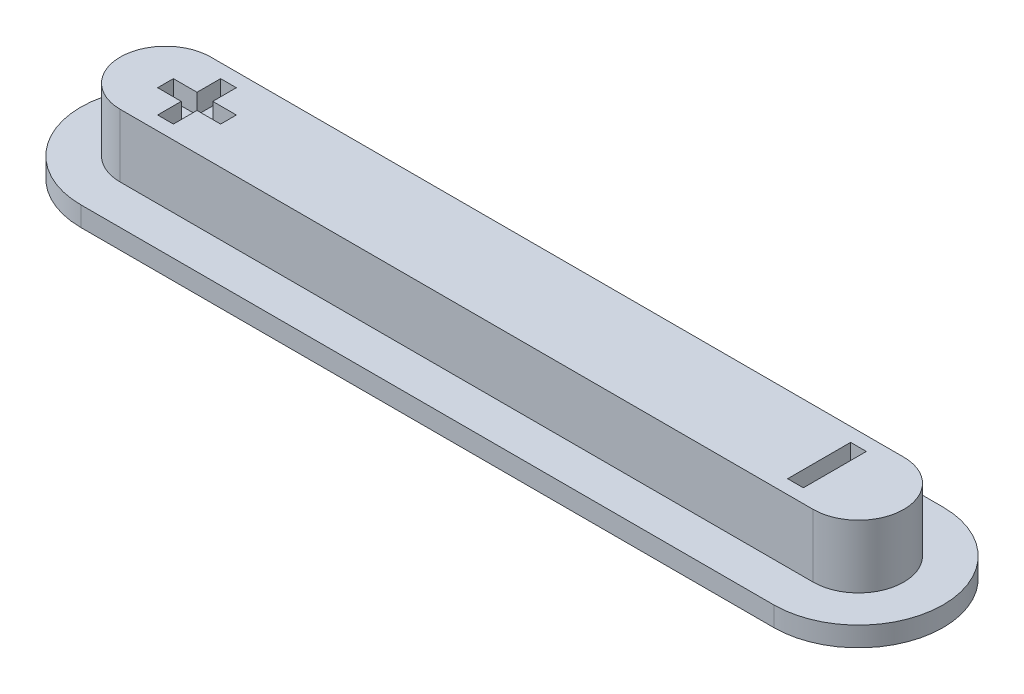
SolidWorks part; units mm, degrees
ref_plane "前视基准面" through (0, 0, 0) normal (0, 0, 1) x (1, 0, 0)
ref_plane "上视基准面" through (0, 0, 0) normal (0, 1, 0) x (1, 0, 0)
ref_plane "右视基准面" through (0, 0, 0) normal (1, 0, 0) x (0, 0, -1)
sketch "草图1" plane through (0, 0, 0) normal (0, 1, 0) x (1, 0, 0)
  line L0 (-8.8, 0) -> (8.8, 0) construction
  line L1 (-8.8, 1.15) -> (8.8, 1.15)
  line L2 (-8.8, -1.15) -> (8.8, -1.15)
  arc A0 (-8.8, 1.15) -> (-8.8, -1.15) centre (-8.8, 0) ccw
  arc A1 (8.8, -1.15) -> (8.8, 1.15) centre (8.8, 0) ccw
  point P2 (0, 0)
extrude "凸台-拉伸1" add sketch "草图1" along normal blind 1.6
sketch "草图2" plane through (0, 0, 0) normal (0, -1, 0) x (1, 0, 0)
  line L4 (-8.8, -2.15) -> (8.8, -2.15)
  line L5 (8.8, 2.15) -> (-8.8, 2.15)
  line L6 (-8.8, -2.15) -> (8.8, -2.15)
  line L7 (8.8, 2.15) -> (-8.8, 2.15)
  arc A4 (-8.8, 2.15) -> (-8.8, -2.15) centre (-8.8, 0) ccw
  arc A5 (8.8, -2.15) -> (8.8, 2.15) centre (8.8, 0) ccw
  arc A6 (-8.8, 2.15) -> (-8.8, -2.15) centre (-8.8, 0) ccw
  arc A7 (8.8, -2.15) -> (8.8, 2.15) centre (8.8, 0) ccw
  dimension "D1" = 1
extrude "凸台-拉伸2" add sketch "草图2" along normal blind 0.5
sketch "草图3" plane through (0, 1.6, 0) normal (0, 1, 0) x (1, 0, 0)
  line L0 (8.8, 1.15) -> (-8.8, 1.15) construction
  line L1 (-8.2, 0.8) -> (-7.8, 0.8)
  line L2 (-8.2, 0.8) -> (-8.2, -0.8)
  line L3 (-8.2, -0.8) -> (-7.8, -0.8)
  line L4 (-7.8, 0.8) -> (-7.8, -0.8)
  line L5 (-8.8, 0.2) -> (-7.2, 0.2)
  line L6 (-8.8, 0.2) -> (-8.8, -0.2)
  line L7 (-8.8, -0.2) -> (-7.2, -0.2)
  line L8 (-7.2, 0.2) -> (-7.2, -0.2)
  line L9 (7.8, 0.8) -> (8.2, 0.8)
  line L10 (7.8, 0.8) -> (7.8, -0.8)
  line L11 (7.8, -0.8) -> (8.2, -0.8)
  line L12 (8.2, 0.8) -> (8.2, -0.8)
  line L13 (-8.8, -1.15) -> (8.8, -1.15) construction
  point P12 (-8, -0.2)
  point P14 (-7.8, 0)
  dimension "D1" = 1.6
  dimension "D2" = 1.6
  dimension "D3" = 1.6
  dimension "D4" = 0.2
  dimension "D5" = 0.4
  dimension "D6" = 0.4
  dimension "D7" = 0.2
  dimension "D8" = 0.35
  dimension "D9" = 0
  dimension "D10" = 0.4
  dimension "D11" = 0.35
  dimension "D12" = 1
extrude "切除-拉伸1" cut sketch "草图3" against normal blind 0.5 contours L12 L9 L10 L11 | L6 L7 L2 L5 | L2 L7 L4 L5 | L2 L5 L4 L1 | L8 L5 L4 L7 | L7 L2 L3 L4
